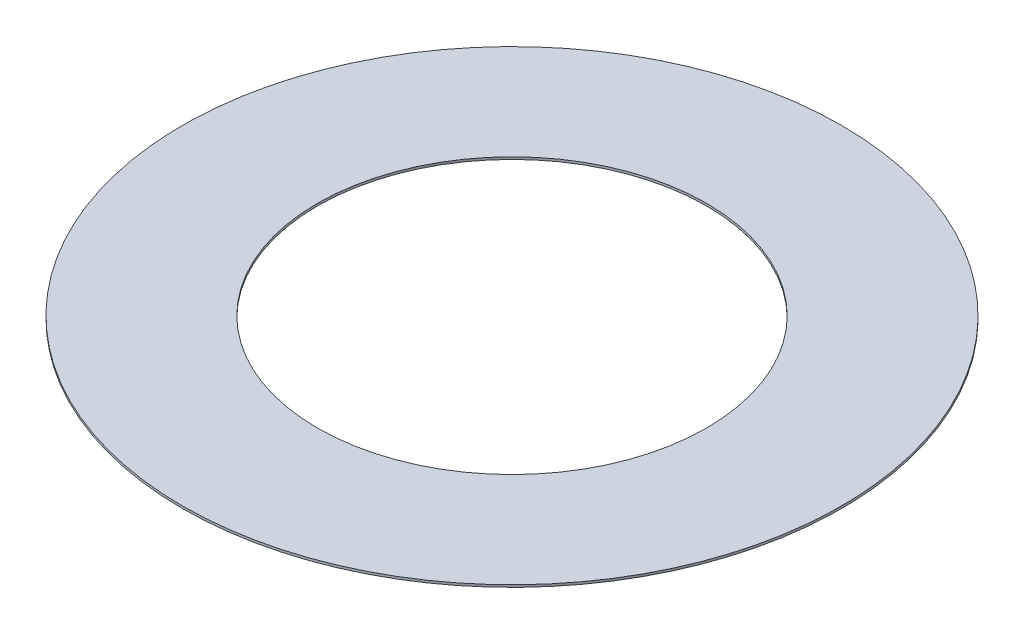
SolidWorks part; units mm, degrees
material "Acrylic (Medium-high impact)"
ref_plane "Front Plane" through (0, 0, 0) normal (0, 0, 1) x (1, 0, 0)
ref_plane "Top Plane" through (0, 0, 0) normal (0, 1, 0) x (1, 0, 0)
ref_plane "Right Plane" through (0, 0, 0) normal (1, 0, 0) x (0, 0, -1)
sketch "Sketch1" plane through (0, 0, 0) normal (0, 1, 0) x (1, 0, 0)
  circle A0 centre (0, 0) radius 25.4
  circle A1 centre (0, 0) radius 14.9987
  dimension "D1" = 50.8
  dimension "D2" = 29.9974
extrude "Boss-Extrude1" add sketch "Sketch1" along normal mid plane 0.1778
